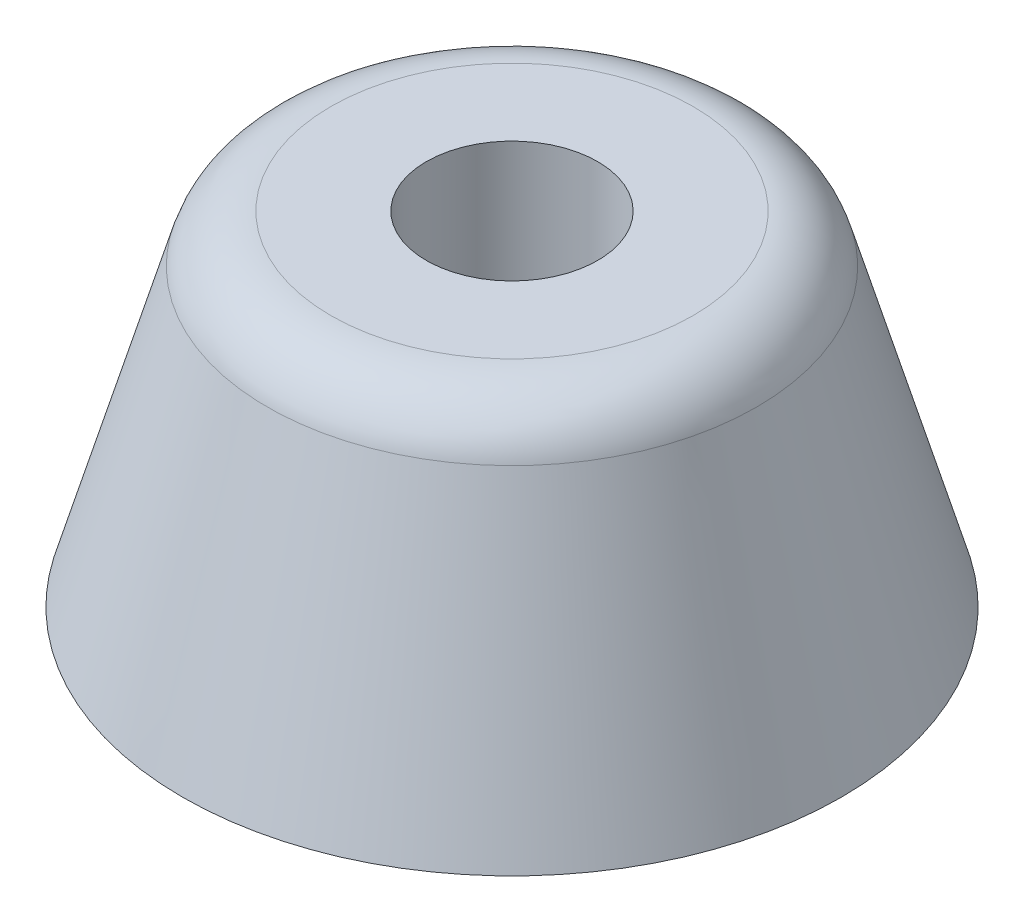
SolidWorks part; units mm, degrees
material "NBR"
ref_plane "前视基准面" through (0, 0, 0) normal (0, 0, 1) x (1, 0, 0)
ref_plane "上视基准面" through (0, 0, 0) normal (0, 1, 0) x (1, 0, 0)
ref_plane "右视基准面" through (0, 0, 0) normal (1, 0, 0) x (0, 0, -1)
ref_plane "基准面1" through (0, 26, 0) normal (0, -1, 0) x (-1, 0, 0)
sketch "草图1" plane through (0, 26, 0) normal (0, -1, 0) x (-1, 0, 0)
  circle A0 centre (0, 0) radius 17.5
  dimension "D1" = 35
sketch "草图2" plane through (0, 0, 0) normal (0, 1, 0) x (1, 0, 0)
  circle A0 centre (0, 0) radius 25
  dimension "D1" = 50
loft "放样1" add profiles "草图1", "草图2"
sketch "草图3" plane through (0, 26, 0) normal (0, 1, 0) x (1, 0, 0)
  circle A0 centre (0, 0) radius 6.5
  dimension "D1" = 13
extrude "切除-拉伸1" cut sketch "草图3" against normal blind 11
sketch "草图4" plane through (0, 15, 0) normal (0, 1, 0) x (1, 0, 0)
  circle A0 centre (0, 0) radius 4
  dimension "D1" = 8
extrude "切除-拉伸2" cut sketch "草图4" against normal up to next
fillet "圆角1" radius 5 1 edges at (17.5, 26, 0)
